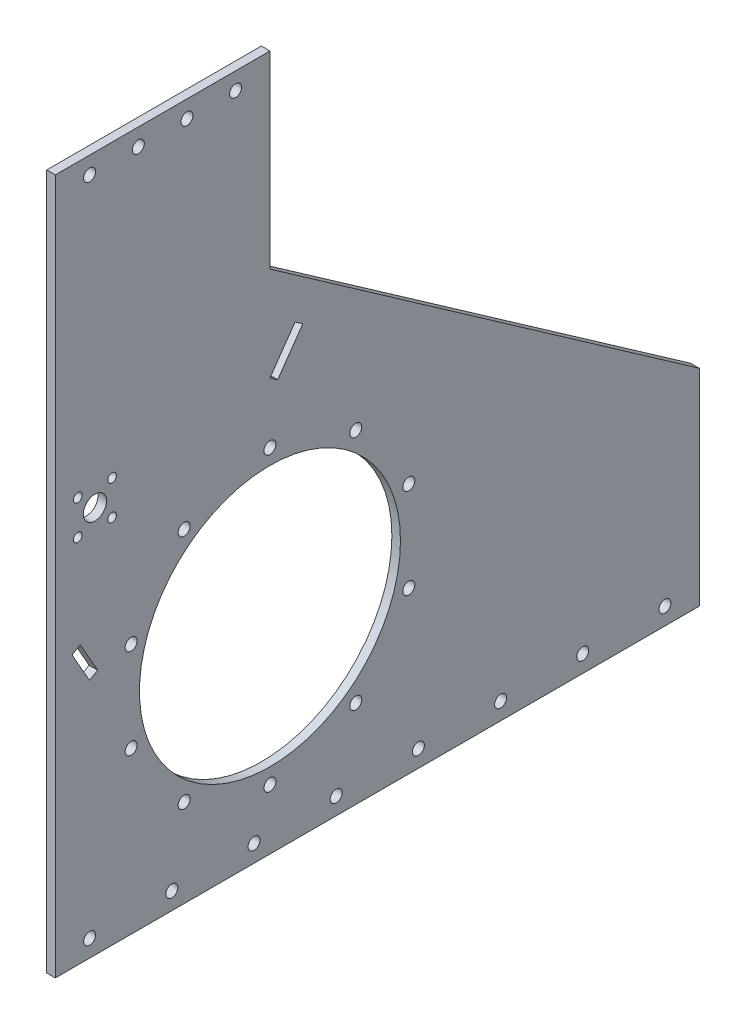
SolidWorks part; units mm, degrees
ref_plane "Ön Düzlem" through (0, 0, 0) normal (0, 0, 1) x (1, 0, 0)
ref_plane "Üst Düzlem" through (0, 0, 0) normal (0, 1, 0) x (1, 0, 0)
ref_plane "Sağ Düzlem" through (0, 0, 0) normal (1, 0, 0) x (0, 0, -1)
sketch "Çizim1" plane through (0, 0, 0) normal (1, 0, 0) x (0, 0, -1)
  line L0 (-250, 350) -> (-250, 570)
  line L1 (-250, -200) -> (500, -200) construction
  line L2 (-250, -200) -> (-250, 350)
  line L3 (-250, 350) -> (0, 350) construction
  line L4 (500, -200) -> (500, 0)
  line L5 (0, 350) -> (0, 0) construction
  line L6 (-76, 131.6359) -> (51.5805, 313.8937) construction
  line L7 (0, 350) -> (500, 0)
  line L8 (0, 350) -> (500, 350) construction
  line L9 (500, 0) -> (500, 350) construction
  line L10 (-250, 570) -> (0, 570)
  line L11 (0, 570) -> (0, 350)
  line L12 (-250, -200) -> (-250, -240)
  line L13 (-250, -240) -> (500, -240)
  line L14 (500, -240) -> (500, -200)
  line L15 (-250, 530) -> (0, 530) construction
  line L16 (-76, 131.6359) -> (-250, 131.6359) construction
  line L17 (-209.3391, 244.13) -> (-77.2372, 137.964) construction
  line L18 (-235.6946, 202.0462) -> (-82.5083, 129.5472) construction
  line L19 (51.5805, 313.8937) -> (60.592, 307.5856) construction
  line L20 (60.592, 307.5856) -> (-55.7265, 141.4162) construction
  line L21 (29.2466, 281.9881) -> (0, 240.2073)
  line L22 (29.2466, 281.9881) -> (38.2581, 275.68)
  line L23 (-131.6359, -76) -> (-250, 132.782) construction
  line L24 (-225, 224.6432) -> (-80.3694, 134.0666) construction
  line L26 (-223.8121, 191.374) -> (-183.8121, 191.374) construction
  line L27 (-223.8121, 191.374) -> (-223.8121, 231.374) construction
  line L28 (-200.6816, 45.7895) -> (-220.9021, 81.4564)
  line L29 (-200.6816, 45.7895) -> (-210.2508, 40.3645)
  line L30 (-220.9021, 81.4564) -> (-230.4713, 76.0314)
  line L31 (-210.2508, 40.3645) -> (-230.4713, 76.0314)
  line L32 (-223.8121, 231.374) -> (-183.8121, 231.374) construction
  line L33 (-183.8121, 191.374) -> (-183.8121, 231.374) construction
  line L34 (-223.8121, 191.374) -> (-183.8121, 231.374) construction
  line L35 (-223.8121, 231.374) -> (-183.8121, 191.374) construction
  line L36 (-233.8121, 181.374) -> (-173.8121, 181.374) construction
  line L37 (-233.8121, 181.374) -> (-233.8121, 241.374) construction
  line L38 (-125, 530) -> (-125, 570) construction
  line L39 (0, 550) -> (-250, 550) construction
  line L40 (125, -200) -> (125, -240) construction
  line L41 (500, -220) -> (-250, -220) construction
  line L42 (0, 0) -> (-76, 131.6359) construction
  line L43 (0, 240.2073) -> (9.0116, 233.8992)
  line L44 (38.2581, 275.68) -> (9.0116, 233.8992)
  line L45 (-230.4713, 76.0314) -> (-250, 110.478) construction
  line L46 (-131.6359, -76) -> (-141.205, -81.425) construction
  line L47 (-210.2508, 40.3645) -> (-141.205, -81.425) construction
  line L48 (-233.8121, 241.374) -> (-173.8121, 241.374) construction
  line L49 (-173.8121, 181.374) -> (-173.8121, 241.374) construction
  line L50 (-233.8121, 181.374) -> (-173.8121, 241.374) construction
  line L51 (-233.8121, 241.374) -> (-173.8121, 181.374) construction
  circle A0 centre (0, 0) radius 150 construction
  circle A1 centre (0, 0) radius 152
  circle A2 centre (-225, 224.6432) radius 25 construction
  circle A3 centre (0, 0) radius 170 construction
  circle A4 centre (0, 170) radius 7
  circle A5 centre (99.9235, 137.5329) radius 7
  circle A6 centre (161.6796, 52.5329) radius 7
  circle A7 centre (161.6796, -52.5329) radius 7
  circle A8 centre (99.9235, -137.5329) radius 7
  circle A9 centre (0, -170) radius 7
  circle A10 centre (-99.9235, -137.5329) radius 7
  circle A11 centre (-161.6796, -52.5329) radius 7
  circle A12 centre (-161.6796, 52.5329) radius 7
  circle A13 centre (-99.9235, 137.5329) radius 7
  circle A14 centre (-80.3694, 134.0666) radius 5 construction
  circle A15 centre (-203.8121, 211.374) radius 13.5
  circle A16 centre (-183.8121, 231.374) radius 5.1
  circle A17 centre (-223.8121, 231.374) radius 5.1
  circle A18 centre (-183.8121, 191.374) radius 5.1
  circle A19 centre (-223.8121, 191.374) radius 5.1
  circle A26 centre (-210, 550) radius 7
  circle A27 centre (-153.3333, 550) radius 7
  circle A28 centre (-96.6667, 550) radius 7
  circle A29 centre (-40, 550) radius 7
  circle A30 centre (0, 0) radius 190 construction
  circle A32 centre (-210, -220) radius 7
  circle A33 centre (-114.2857, -220) radius 7
  circle A34 centre (-18.5714, -220) radius 7
  circle A35 centre (77.1429, -220) radius 7
  circle A36 centre (172.8571, -220) radius 7
  circle A37 centre (268.5714, -220) radius 7
  circle A38 centre (364.2857, -220) radius 7
  circle A39 centre (460, -220) radius 7
  point P58 (0, 0)
  point P88 (-125, 550)
  point P105 (125, -220)
  dimension "D1" = 300
  dimension "D3" = 500
  dimension "D4" = 304
  dimension "D5" = 250
  dimension "D11" = 200
  dimension "D23" = 27
  dimension "D24" = 340
  dimension "D25" = 14
  dimension "D27" = 170.6521
  dimension "D29" = 40
  dimension "D33" = 40
  dimension "D34" = 380
  dimension "D35" = 40
  dimension "D37" = 40
  dimension "D38" = 10.2
  dimension "D19" = 10
  dimension "D20" = 50
  dimension "D30" = 14
  dimension "D39" = 60
  dimension "D2" = 550
  dimension "D6" = 250
  dimension "D7" = 240
  dimension "D8" = 30
  dimension "D9" = 11
  dimension "D10" = 51
  dimension "D12" = 220
  dimension "D13" = 40
  dimension "D14" = 40
  dimension "D15" = 222.474
  dimension "D16" = 140
  dimension "D17" = 90
  dimension "D18" = 11
  dimension "D21" = 41
  dimension "D22" = 240
  dimension "D28" = 46.1879
  dimension "D31" = 40
  dimension "D40" = 38.9457
  dimension "D41" = 59
  dimension "D42" = 750
  dimension "D32" = 4
  dimension "D36" = 8
  dimension "D26" = 10
extrude "Yükseklik-Ekstrüzyon1" add sketch "Çizim1" along normal blind 10
